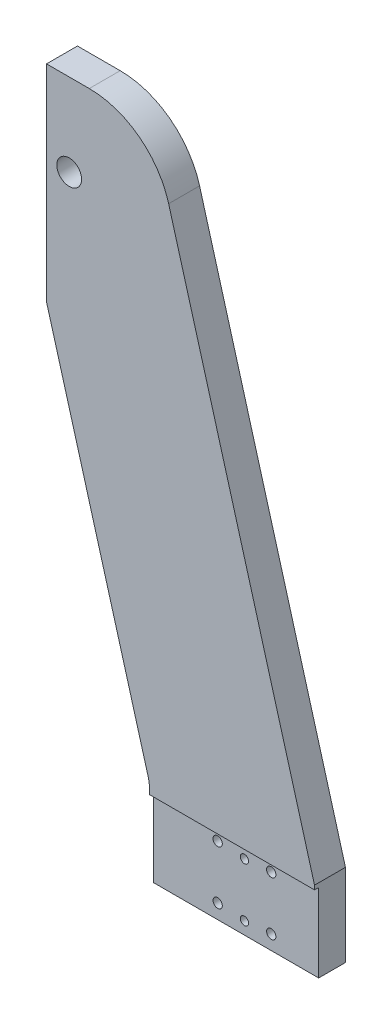
SolidWorks part; units mm, degrees
ref_plane "Alzado" through (0, 0, 0) normal (0, 0, 1) x (1, 0, 0)
ref_plane "Planta" through (0, 0, 0) normal (0, 1, 0) x (1, 0, 0)
ref_plane "Vista lateral" through (0, 0, 0) normal (1, 0, 0) x (0, 0, -1)
sketch "Croquis1" plane through (0, 0, 0) normal (0, 0, 1) x (1, 0, 0)
  line L0 (80, 0) -> (80, 40)
  line L1 (-50, 320) -> (-29.2688, 320)
  line L2 (-50, 320) -> (-50, 220)
  line L3 (0, 0) -> (80, 0)
  line L4 (9.2285, 290.8607) -> (80, 40)
  line L9 (-50, 220) -> (-0.7513, 45.4303)
  line L11 (0, 40) -> (0, 0)
  arc A2 (9.2285, 290.8607) -> (-29.2688, 320) centre (-29.2688, 280) ccw
  arc A3 (-0.7513, 45.4303) -> (0, 40) centre (-20, 40) cw
  dimension "D7" = 40
  dimension "D9" = 40
  dimension "D4" = 20
  dimension "D1" = 50
  dimension "D2" = 320
  dimension "D3" = 80
  dimension "D5" = 100
  dimension "D6" = 40
extrude "Saliente-Extruir1" add sketch "Croquis1" along normal blind 15
sketch "Croquis2" plane through (0, 0, 0) normal (0, 0, -1) x (-1, 0, 0)
  line L0 (29.2688, 320) -> (50, 320) construction
  line L2 (50, 320) -> (50, 220) construction
  circle A0 centre (39, 280) radius 6
  dimension "D3" = 12
  dimension "D1" = 40
  dimension "D2" = 11
extrude "Cortar-Extruir1" cut sketch "Croquis2" against normal through all
hole_wizard "Perforador para roscar para macho de roscar para M44" positions "Croquis7" profile "Croquis8" hole size "M4" standard "DIN"
sketch "Croquis7" plane through (0, 0, 0) normal (0, 0, -1) x (-1, 0, 0)
  line L0 (39, 298.25) -> (39, 261.75)
  circle A0 centre (39, 280) radius 6 construction
  point P10 (39, 298.25)
  point P12 (39, 261.75)
  dimension "D1" = 18.25
  dimension "D2" = 18.25
sketch "Croquis8" plane through (-39, 261.75, 0) normal (1, 0, 0) x (0, 1, 0)
  line L0 (0, 0) -> (0, 7.9914)
  line L1 (0, 7.9914) -> (1.65, 7)
  line L2 (1.65, 7) -> (1.65, 0)
  line L5 (1.65, 0) -> (0, 0)
  line L10 (0, 7.9914) -> (-1.65, 7) construction
  line L11 (0, -6.35) -> (0, 107.95) construction
  dimension "Diámetro de taladro" = 3.3
  dimension "Profundidad de taladro" = 7
  dimension "Ángulo de perforador" = 118
sketch "Croquis9" plane through (0, 0, 15) normal (0, 0, 1) x (1, 0, 0)
  line L1 (0, 0) -> (80, 0)
  line L2 (0, 0) -> (0, 38)
  line L3 (0, 38) -> (80, 38)
  line L4 (80, 0) -> (80, 38)
  dimension "D1" = 80
  dimension "D2" = 38
extrude "Cortar-Extruir2" cut sketch "Croquis9" against normal blind 2
hole_wizard "Taladros de espiga de Ø4.0mm1" positions "Croquis10" profile "Croquis12" hole size "Ø4.0" standard "DIN"
sketch "Croquis10" plane through (-50, 0, 0) normal (-1, 0, 0) x (0, 0, 1)
  line L0 (0, 320) -> (0, 220) construction
  line L1 (15, 320) -> (0, 320) construction
  line L2 (0, 240) -> (15, 240) construction
  line L3 (15, 320) -> (15, 220) construction
  point P0 (6, 304)
  point P2 (6, 256)
  dimension "D1" = 6
  dimension "D2" = 6
  dimension "D3" = 16
  dimension "D4" = 16
  dimension "D5" = 80
sketch "Croquis12" plane through (-50, 304, 6) normal (0, 1, 0) x (0, 0, 1)
  line L0 (0, 0) -> (0, 18.2017)
  line L1 (0, 18.2017) -> (2, 17)
  line L2 (2, 17) -> (2, 0)
  line L5 (2, 0) -> (0, 0)
  line L10 (0, 18.2017) -> (-2, 17) construction
  line L11 (0, -6.35) -> (0, 107.95) construction
  dimension "Diámetro de taladro" = 4
  dimension "Profundidad de taladro" = 17
  dimension "Ángulo de perforador" = 118
hole_wizard "Taladro roscado M41" positions "Croquis13" profile "Croquis14" tap size "M4" standard "DIN"
sketch "Croquis13" plane through (-50, 0, 0) normal (-1, 0, 0) x (0, 0, 1)
  line L0 (0, 320) -> (0, 220) construction
  line L1 (15, 320) -> (0, 320) construction
  line L2 (0, 240) -> (15, 240) construction
  line L3 (15, 320) -> (15, 220) construction
  line L5 (6, 240) -> (6, 320) construction
  point P0 (6, 312)
  point P2 (6, 248)
  point P15 (6, 291)
  point P17 (6, 269)
  point P24 (4.5665, 311.9996)
  point P25 (4.4072, 287.5224)
  point P26 (4.3489, 257.4686)
  point P27 (4.3306, 248)
  dimension "D1" = 6
  dimension "D2" = 29
  dimension "D3" = 8
  dimension "D4" = 8
  dimension "D5" = 80
  dimension "D6" = 29
sketch "Croquis14" plane through (-50, 312, 6) normal (0, 1, 0) x (0, 0, 1)
  line L0 (0, 0) -> (0, 12.4914)
  line L1 (0, 12.4914) -> (1.65, 11.5)
  line L2 (1.65, 11.5) -> (1.65, 0)
  line L5 (1.65, 0) -> (0, 0)
  line L10 (0, 12.4914) -> (-1.65, 11.5) construction
  line L11 (0, -6.35) -> (0, 107.95) construction
  dimension "Diámetro de perforador para roscar" = 3.3
  dimension "Profundidad de perforador para roscar" = 11.5
  dimension "Ángulo de perforador" = 118
cosmetic thread "Rosca de taladro1" parameters "D1"=8, "D2"=4
cosmetic thread "Rosca de taladro2" parameters "D1"=8, "D2"=4
cosmetic thread "Rosca de taladro3" parameters "D1"=8, "D2"=4
cosmetic thread "Rosca de taladro4" parameters "D1"=8, "D2"=4
hole_wizard "Refrentado para tornillo con cabeza hueca de M41" positions "Croquis15" profile "Croquis16" counterbore size "M4" standard "DIN" end condition through all
sketch "Croquis15" plane through (0, 0, 0) normal (0, 0, -1) x (-1, 0, 0)
  line L1 (-57, 7) -> (-31, 7)
  line L2 (-57, 7) -> (-57, 33)
  line L3 (-57, 33) -> (-31, 33)
  line L4 (-31, 7) -> (-31, 33)
  line L5 (-57, 7) -> (-31, 33) construction
  line L6 (-57, 33) -> (-31, 7) construction
  line L16 (0, 0) -> (-80, 0) construction
  line L17 (-80, 0) -> (-80, 40) construction
  point P148 (-57, 33)
  point P151 (-31, 33)
  point P154 (-31, 7)
  point P157 (-57, 7)
  dimension "D1" = 26
  dimension "D2" = 26
  dimension "D3" = 23
  dimension "D4" = 7
sketch "Croquis16" plane through (57, 7, 0) normal (1, 0, 0) x (0, 1, 0)
  line L0 (0, 0) -> (0, 15)
  line L1 (0, 15) -> (2.25, 15)
  line L3 (2.25, 15) -> (2.25, 4.4)
  line L4 (2.25, 4.4) -> (4, 4.4)
  line L5 (4, 4.4) -> (4, 0)
  line L7 (4, 0) -> (0, 0)
  line L11 (0, -6.35) -> (0, 107.95) construction
  dimension "Diámetro de taladro hasta el siguiente" = 4.5
  dimension "Profundidad de taladro hasta el siguiente" = 15
  dimension "Diámetro de refrentado" = 8
  dimension "Profundidad de refrentado" = 4.4
hole_wizard "Taladros de espiga de Ø4.0mm2" positions "Croquis17" profile "Croquis18" hole size "Ø4.0" standard "DIN" end condition through all
sketch "Croquis17" plane through (0, 0, 0) normal (0, 0, -1) x (-1, 0, 0)
  line L0 (-44, 32) -> (-44, 6) construction
  line L2 (0, 0) -> (-80, 0) construction
  line L3 (-80, 0) -> (-80, 40) construction
  point P0 (-44, 32)
  point P2 (-44, 6)
  dimension "D1" = 26
  dimension "D2" = 6
  dimension "D3" = 36
sketch "Croquis18" plane through (44, 32, 0) normal (1, 0, 0) x (0, 1, 0)
  line L0 (0, 0) -> (0, 15)
  line L1 (0, 15) -> (2, 15)
  line L2 (2, 15) -> (2, 0)
  line L5 (2, 0) -> (0, 0)
  line L11 (0, -6.35) -> (0, 107.95) construction
  dimension "Diámetro de taladro hasta el siguiente" = 4
  dimension "Profundidad de taladro hasta el siguiente" = 15
